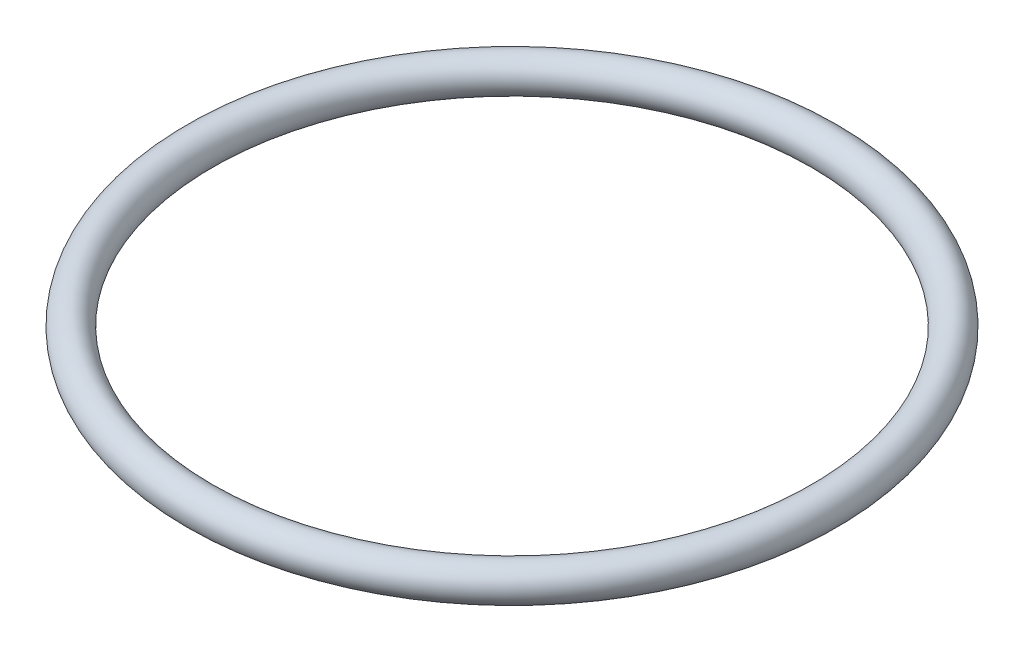
SolidWorks part; units mm, degrees
ref_plane "Front Plane" through (0, 0, 0) normal (0, 0, 1) x (1, 0, 0)
ref_plane "Top Plane" through (0, 0, 0) normal (0, 1, 0) x (1, 0, 0)
ref_plane "Right Plane" through (0, 0, 0) normal (1, 0, 0) x (0, 0, -1)
sketch "Sketch1" plane through (0, 0, 0) normal (0, 0, 1) x (1, 0, 0)
  line L0 (0, 0) -> (-35.5, 0) construction
  line L1 (0, 0) -> (0, 13.0407)
  circle A0 centre (-35.5, 0) radius 2
  dimension "D1" = 35.5
revolve "Revolve1" add sketch "Sketch1" angle 360 about L1
sketch "Sketch2" plane through (0, 0, 0) normal (0, 1, 0) x (1, 0, 0)
  circle A0 centre (0, 0) radius 33.5
  dimension "D1" = 67
